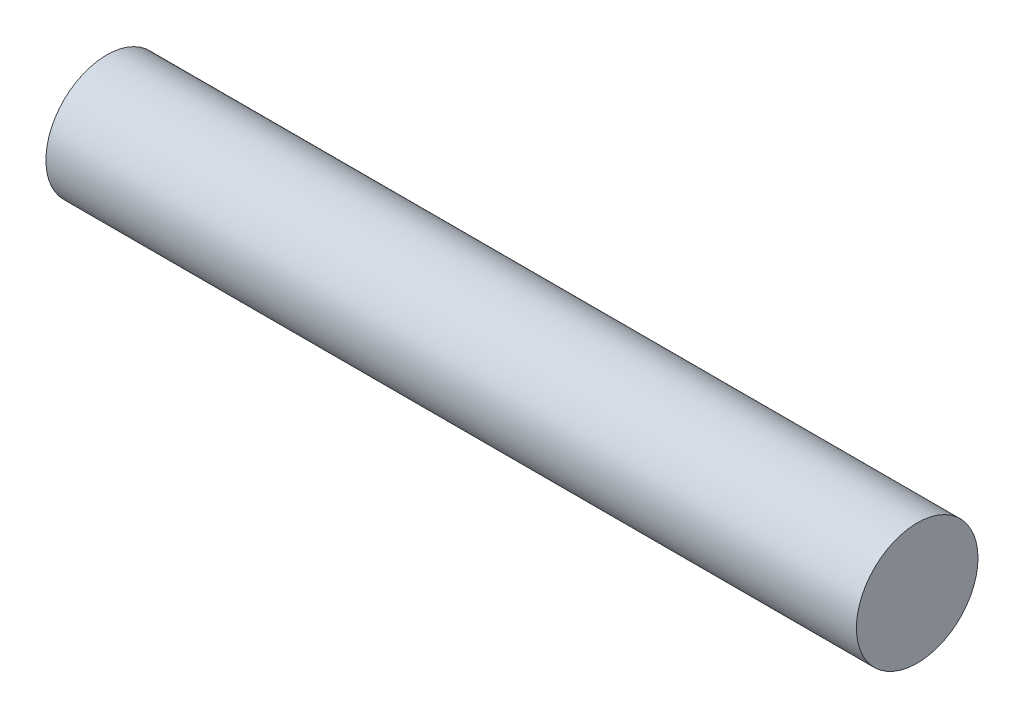
SolidWorks part; units mm, degrees
material "6061 Alloy"
ref_plane "Front Plane" through (0, 0, 0) normal (0, 0, 1) x (1, 0, 0)
ref_plane "Top Plane" through (0, 0, 0) normal (0, 1, 0) x (1, 0, 0)
ref_plane "Right Plane" through (0, 0, 0) normal (1, 0, 0) x (0, 0, -1)
sketch "Sketch1" plane through (0, 0, 0) normal (1, 0, 0) x (0, 0, -1)
  circle A0 centre (0, 0) radius 0.75
  dimension "D1" = 1.5
extrude "Boss-Extrude1" add sketch "Sketch1" along normal blind 10
ref_plane "Mid Point Plane Reference" through (5, 0, 0) normal (1, 0, 0) x (0, 0, -1)
